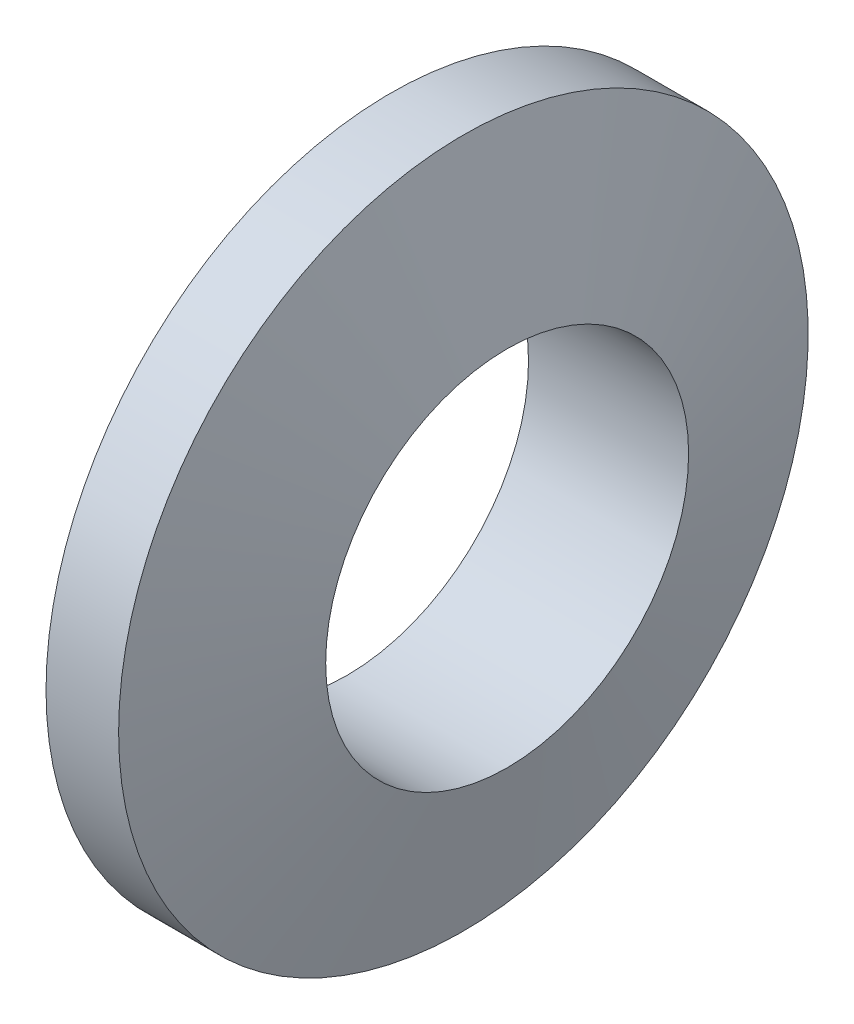
SolidWorks part; units mm, degrees
ref_plane "Спереди" through (0, 0, 0) normal (0, 0, 1) x (1, 0, 0)
ref_plane "Сверху" through (0, 0, 0) normal (0, 1, 0) x (1, 0, 0)
ref_plane "Справа" through (0, 0, 0) normal (1, 0, 0) x (0, 0, -1)
sketch "Ske" plane through (0, 0, 0) normal (0, 0, 1) x (1, 0, 0)
  line L0 (-10, 0) -> (10, 0) construction
  line L1 (0, 0) -> (0, 9.5) construction
  line L2 (-1, 9.5) -> (1, 9.5)
  line L3 (1, 9.5) -> (2.2058, 5)
  line L4 (-2.2058, 5) -> (2.2058, 5)
  line L5 (-1, 9.5) -> (-2.2058, 5)
  dimension "D1" = 19
  dimension "d" = 10
  dimension "b2" = 2
  dimension "D4" = 30
revolve "Основание-Повернуть" add sketch "Ske" angle 360 about L0
